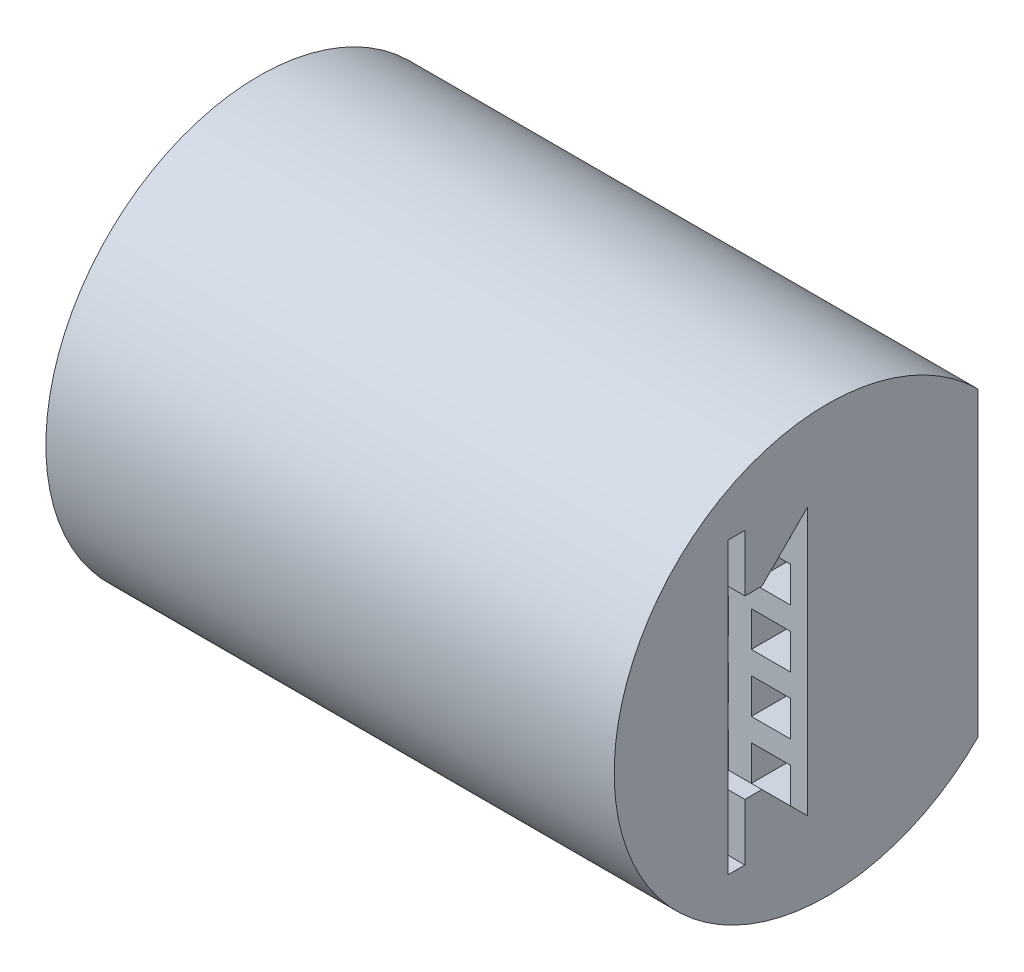
SolidWorks part; units mm, degrees
ref_plane "Front Plane" through (0, 0, 0) normal (0, 0, 1) x (1, 0, 0)
ref_plane "Top Plane" through (0, 0, 0) normal (0, 1, 0) x (1, 0, 0)
ref_plane "Right Plane" through (0, 0, 0) normal (1, 0, 0) x (0, 0, -1)
sketch "Sketch1" plane through (0, 0, 0) normal (1, 0, 0) x (0, 0, -1)
  line L1 (5.3033, 5.3033) -> (5.3033, -5.3033)
  line L14 (5.3033, 5.3033) -> (8.7403, 1.8663) construction
  line L15 (-3.5, -5.1) -> (-3.5, 5.1)
  line L16 (-3.5, 5.1) -> (-2.9, 5.1)
  line L17 (-2.9, 5.1) -> (-2.9, 3.1)
  line L18 (-2.9, 3.1) -> (-2.3, 3.1)
  line L19 (-2.3, 3.1) -> (-0.6967, 4.7033)
  line L20 (17.1404, 0) -> (-17.1404, 0) construction
  line L21 (-0.6967, 4.7033) -> (-0.6967, -4.7033)
  line L22 (-0.6967, 4.7033) -> (5.3033, 4.7033) construction
  line L23 (-3.5, -5.1) -> (-2.9, -5.1)
  line L24 (-2.9, -5.1) -> (-2.9, -3.1)
  line L25 (-2.9, -3.1) -> (-2.3, -3.1)
  line L26 (-2.3, -3.1) -> (-0.6967, -4.7033)
  circle A2 centre (0, 0) radius 7.5 construction
  arc A4 (5.3033, 5.3033) -> (5.3033, -5.3033) centre (0, 0) ccw
  point P13 (0, 0)
  point P14 (-17.1404, 0)
  point P15 (-1.4227, 0)
  point P17 (-3.1802, 0)
  point P18 (-0.7891, 0)
  point P20 (-3.5, 0)
  point P24 (-0.6967, 0)
  dimension "D2" = 45
  dimension "D1" = 15
  dimension "D3" = 5.1
  dimension "D4" = 0.6
  dimension "D5" = 2
  dimension "D6" = 0.6
  dimension "D7" = 45
  dimension "D8" = 0.6
  dimension "D9" = 6
extrude "Boss-Extrude1" add sketch "Sketch1" along normal mid plane 20
sketch "Sketch2" plane through (0, 0, -5.3033) normal (0, 0, -1) x (-1, 0, 0)
  line L0 (9.4, -4.7033) -> (9.4, 4.7033) construction
  line L1 (9.4, 4.7033) -> (-9.4, 4.7033) construction
  line L2 (-9.4, 4.7033) -> (-9.4, -4.7033) construction
  line L3 (-9.4, -4.7033) -> (9.4, -4.7033) construction
  line L4 (10, -5.3033) -> (10, 5.3033)
  line L5 (10, 5.3033) -> (-10, 5.3033)
  line L6 (-10, 5.3033) -> (-10, -5.3033)
  line L7 (-10, -5.3033) -> (10, -5.3033)
  line L8 (10, -5.3033) -> (10, 5.3033) construction
  line L9 (10, 5.3033) -> (-10, 5.3033) construction
  line L10 (-10, 5.3033) -> (-10, -5.3033) construction
  line L11 (-10, -5.3033) -> (10, -5.3033) construction
  line L12 (-7.2222, -4.7033) -> (-7.2222, -3.462)
  line L19 (-9.4, -4.7033) -> (-8.0222, -4.7033)
  line L20 (-9.4, -4.7033) -> (-9.4, -3.462)
  line L21 (-9.4, -3.462) -> (-8.0222, -3.462)
  line L22 (-8.0222, -4.7033) -> (-8.0222, -3.462)
  line L23 (-7.2222, -4.7033) -> (-5.8444, -4.7033)
  line L24 (-5.8444, -4.7033) -> (-5.8444, -3.462)
  line L25 (-7.2222, -3.462) -> (-5.8444, -3.462)
  line L26 (-7.2222, -2.662) -> (-7.2222, -1.4207)
  line L27 (-7.2222, -2.662) -> (-5.8444, -2.662)
  line L28 (-5.8444, -2.662) -> (-5.8444, -1.4207)
  line L29 (-7.2222, -1.4207) -> (-5.8444, -1.4207)
  line L30 (-7.2222, -0.6207) -> (-7.2222, 0.6207)
  line L31 (-7.2222, -0.6207) -> (-5.8444, -0.6207)
  line L32 (-5.8444, -0.6207) -> (-5.8444, 0.6207)
  line L33 (-7.2222, 0.6207) -> (-5.8444, 0.6207)
  line L34 (-9.4, -2.662) -> (-9.4, -1.4207)
  line L35 (-9.4, -2.662) -> (-8.0222, -2.662)
  line L36 (-8.0222, -2.662) -> (-8.0222, -1.4207)
  line L37 (-9.4, -1.4207) -> (-8.0222, -1.4207)
  line L38 (-9.4, -0.6207) -> (-9.4, 0.6207)
  line L39 (-9.4, -0.6207) -> (-8.0222, -0.6207)
  line L40 (-8.0222, -0.6207) -> (-8.0222, 0.6207)
  line L41 (-9.4, 0.6207) -> (-8.0222, 0.6207)
  line L42 (-5.0444, -4.7033) -> (-5.0444, -3.462)
  line L43 (-5.0444, -4.7033) -> (-3.6667, -4.7033)
  line L44 (-3.6667, -4.7033) -> (-3.6667, -3.462)
  line L45 (-5.0444, -3.462) -> (-3.6667, -3.462)
  line L46 (-2.8667, -4.7033) -> (-2.8667, -3.462)
  line L47 (-2.8667, -4.7033) -> (-1.4889, -4.7033)
  line L48 (-1.4889, -4.7033) -> (-1.4889, -3.462)
  line L49 (-2.8667, -3.462) -> (-1.4889, -3.462)
  line L50 (-0.6889, -4.7033) -> (-0.6889, -3.462)
  line L51 (-0.6889, -4.7033) -> (0.6889, -4.7033)
  line L52 (0.6889, -4.7033) -> (0.6889, -3.462)
  line L53 (-0.6889, -3.462) -> (0.6889, -3.462)
  line L54 (1.4889, -4.7033) -> (1.4889, -3.462)
  line L55 (1.4889, -4.7033) -> (2.8667, -4.7033)
  line L56 (2.8667, -4.7033) -> (2.8667, -3.462)
  line L57 (1.4889, -3.462) -> (2.8667, -3.462)
  line L58 (3.6667, -4.7033) -> (3.6667, -3.462)
  line L59 (3.6667, -4.7033) -> (5.0444, -4.7033)
  line L60 (5.0444, -4.7033) -> (5.0444, -3.462)
  line L61 (3.6667, -3.462) -> (5.0444, -3.462)
  line L62 (5.8444, -4.7033) -> (5.8444, -3.462)
  line L63 (5.8444, -4.7033) -> (7.2222, -4.7033)
  line L64 (7.2222, -4.7033) -> (7.2222, -3.462)
  line L65 (5.8444, -3.462) -> (7.2222, -3.462)
  line L66 (8.0222, -4.7033) -> (8.0222, -3.462)
  line L67 (8.0222, -4.7033) -> (9.4, -4.7033)
  line L68 (9.4, -4.7033) -> (9.4, -3.462)
  line L69 (8.0222, -3.462) -> (9.4, -3.462)
  line L82 (-5.0444, -2.662) -> (-5.0444, -1.4207)
  line L83 (-5.0444, -2.662) -> (-3.6667, -2.662)
  line L84 (-3.6667, -2.662) -> (-3.6667, -1.4207)
  line L85 (-5.0444, -1.4207) -> (-3.6667, -1.4207)
  line L86 (-2.8667, -2.662) -> (-2.8667, -1.4207)
  line L87 (-2.8667, -2.662) -> (-1.4889, -2.662)
  line L88 (-1.4889, -2.662) -> (-1.4889, -1.4207)
  line L89 (-2.8667, -1.4207) -> (-1.4889, -1.4207)
  line L90 (-0.6889, -2.662) -> (-0.6889, -1.4207)
  line L91 (-0.6889, -2.662) -> (0.6889, -2.662)
  line L92 (0.6889, -2.662) -> (0.6889, -1.4207)
  line L93 (-0.6889, -1.4207) -> (0.6889, -1.4207)
  line L94 (1.4889, -2.662) -> (1.4889, -1.4207)
  line L95 (1.4889, -2.662) -> (2.8667, -2.662)
  line L96 (2.8667, -2.662) -> (2.8667, -1.4207)
  line L97 (1.4889, -1.4207) -> (2.8667, -1.4207)
  line L98 (3.6667, -2.662) -> (3.6667, -1.4207)
  line L99 (3.6667, -2.662) -> (5.0444, -2.662)
  line L100 (5.0444, -2.662) -> (5.0444, -1.4207)
  line L101 (3.6667, -1.4207) -> (5.0444, -1.4207)
  line L102 (5.8444, -2.662) -> (5.8444, -1.4207)
  line L103 (5.8444, -2.662) -> (7.2222, -2.662)
  line L104 (7.2222, -2.662) -> (7.2222, -1.4207)
  line L105 (5.8444, -1.4207) -> (7.2222, -1.4207)
  line L106 (8.0222, -2.662) -> (8.0222, -1.4207)
  line L107 (8.0222, -2.662) -> (9.4, -2.662)
  line L108 (9.4, -2.662) -> (9.4, -1.4207)
  line L109 (8.0222, -1.4207) -> (9.4, -1.4207)
  line L122 (-5.0444, -0.6207) -> (-5.0444, 0.6207)
  line L123 (-5.0444, -0.6207) -> (-3.6667, -0.6207)
  line L124 (-3.6667, -0.6207) -> (-3.6667, 0.6207)
  line L125 (-5.0444, 0.6207) -> (-3.6667, 0.6207)
  line L126 (-2.8667, -0.6207) -> (-2.8667, 0.6207)
  line L127 (-2.8667, -0.6207) -> (-1.4889, -0.6207)
  line L128 (-1.4889, -0.6207) -> (-1.4889, 0.6207)
  line L129 (-2.8667, 0.6207) -> (-1.4889, 0.6207)
  line L130 (-0.6889, -0.6207) -> (-0.6889, 0.6207)
  line L131 (-0.6889, -0.6207) -> (0.6889, -0.6207)
  line L132 (0.6889, -0.6207) -> (0.6889, 0.6207)
  line L133 (-0.6889, 0.6207) -> (0.6889, 0.6207)
  line L134 (1.4889, -0.6207) -> (1.4889, 0.6207)
  line L135 (1.4889, -0.6207) -> (2.8667, -0.6207)
  line L136 (2.8667, -0.6207) -> (2.8667, 0.6207)
  line L137 (1.4889, 0.6207) -> (2.8667, 0.6207)
  line L138 (3.6667, -0.6207) -> (3.6667, 0.6207)
  line L139 (3.6667, -0.6207) -> (5.0444, -0.6207)
  line L140 (5.0444, -0.6207) -> (5.0444, 0.6207)
  line L141 (3.6667, 0.6207) -> (5.0444, 0.6207)
  line L142 (5.8444, -0.6207) -> (5.8444, 0.6207)
  line L143 (5.8444, -0.6207) -> (7.2222, -0.6207)
  line L144 (7.2222, -0.6207) -> (7.2222, 0.6207)
  line L145 (5.8444, 0.6207) -> (7.2222, 0.6207)
  line L146 (8.0222, -0.6207) -> (8.0222, 0.6207)
  line L147 (8.0222, -0.6207) -> (9.4, -0.6207)
  line L148 (9.4, -0.6207) -> (9.4, 0.6207)
  line L149 (8.0222, 0.6207) -> (9.4, 0.6207)
  line L150 (-9.4, 1.4207) -> (-9.4, 2.662)
  line L151 (-9.4, 1.4207) -> (-8.0222, 1.4207)
  line L152 (-8.0222, 1.4207) -> (-8.0222, 2.662)
  line L153 (-9.4, 2.662) -> (-8.0222, 2.662)
  line L154 (-7.2222, 1.4207) -> (-7.2222, 2.662)
  line L155 (-7.2222, 1.4207) -> (-5.8444, 1.4207)
  line L156 (-5.8444, 1.4207) -> (-5.8444, 2.662)
  line L157 (-7.2222, 2.662) -> (-5.8444, 2.662)
  line L158 (-5.0444, 1.4207) -> (-5.0444, 2.662)
  line L159 (-5.0444, 1.4207) -> (-3.6667, 1.4207)
  line L160 (-3.6667, 1.4207) -> (-3.6667, 2.662)
  line L161 (-5.0444, 2.662) -> (-3.6667, 2.662)
  line L162 (-2.8667, 1.4207) -> (-2.8667, 2.662)
  line L163 (-2.8667, 1.4207) -> (-1.4889, 1.4207)
  line L164 (-1.4889, 1.4207) -> (-1.4889, 2.662)
  line L165 (-2.8667, 2.662) -> (-1.4889, 2.662)
  line L166 (-0.6889, 1.4207) -> (-0.6889, 2.662)
  line L167 (-0.6889, 1.4207) -> (0.6889, 1.4207)
  line L168 (0.6889, 1.4207) -> (0.6889, 2.662)
  line L169 (-0.6889, 2.662) -> (0.6889, 2.662)
  line L170 (1.4889, 1.4207) -> (1.4889, 2.662)
  line L171 (1.4889, 1.4207) -> (2.8667, 1.4207)
  line L172 (2.8667, 1.4207) -> (2.8667, 2.662)
  line L173 (1.4889, 2.662) -> (2.8667, 2.662)
  line L174 (3.6667, 1.4207) -> (3.6667, 2.662)
  line L175 (3.6667, 1.4207) -> (5.0444, 1.4207)
  line L176 (5.0444, 1.4207) -> (5.0444, 2.662)
  line L177 (3.6667, 2.662) -> (5.0444, 2.662)
  line L178 (5.8444, 1.4207) -> (5.8444, 2.662)
  line L179 (5.8444, 1.4207) -> (7.2222, 1.4207)
  line L180 (7.2222, 1.4207) -> (7.2222, 2.662)
  line L181 (5.8444, 2.662) -> (7.2222, 2.662)
  line L182 (8.0222, 1.4207) -> (8.0222, 2.662)
  line L183 (8.0222, 1.4207) -> (9.4, 1.4207)
  line L184 (9.4, 1.4207) -> (9.4, 2.662)
  line L185 (8.0222, 2.662) -> (9.4, 2.662)
  line L186 (-9.4, 3.462) -> (-9.4, 4.7033)
  line L187 (-9.4, 3.462) -> (-8.0222, 3.462)
  line L188 (-8.0222, 3.462) -> (-8.0222, 4.7033)
  line L189 (-9.4, 4.7033) -> (-8.0222, 4.7033)
  line L190 (-7.2222, 3.462) -> (-7.2222, 4.7033)
  line L191 (-7.2222, 3.462) -> (-5.8444, 3.462)
  line L192 (-5.8444, 3.462) -> (-5.8444, 4.7033)
  line L193 (-7.2222, 4.7033) -> (-5.8444, 4.7033)
  line L194 (-5.0444, 3.462) -> (-5.0444, 4.7033)
  line L195 (-5.0444, 3.462) -> (-3.6667, 3.462)
  line L196 (-3.6667, 3.462) -> (-3.6667, 4.7033)
  line L197 (-5.0444, 4.7033) -> (-3.6667, 4.7033)
  line L198 (-2.8667, 3.462) -> (-2.8667, 4.7033)
  line L199 (-2.8667, 3.462) -> (-1.4889, 3.462)
  line L200 (-1.4889, 3.462) -> (-1.4889, 4.7033)
  line L201 (-2.8667, 4.7033) -> (-1.4889, 4.7033)
  line L202 (-0.6889, 3.462) -> (-0.6889, 4.7033)
  line L203 (-0.6889, 3.462) -> (0.6889, 3.462)
  line L204 (0.6889, 3.462) -> (0.6889, 4.7033)
  line L205 (-0.6889, 4.7033) -> (0.6889, 4.7033)
  line L206 (1.4889, 3.462) -> (1.4889, 4.7033)
  line L207 (1.4889, 3.462) -> (2.8667, 3.462)
  line L208 (2.8667, 3.462) -> (2.8667, 4.7033)
  line L209 (1.4889, 4.7033) -> (2.8667, 4.7033)
  line L210 (3.6667, 3.462) -> (3.6667, 4.7033)
  line L211 (3.6667, 3.462) -> (5.0444, 3.462)
  line L212 (5.0444, 3.462) -> (5.0444, 4.7033)
  line L213 (3.6667, 4.7033) -> (5.0444, 4.7033)
  line L214 (5.8444, 3.462) -> (5.8444, 4.7033)
  line L215 (5.8444, 3.462) -> (7.2222, 3.462)
  line L216 (7.2222, 3.462) -> (7.2222, 4.7033)
  line L217 (5.8444, 4.7033) -> (7.2222, 4.7033)
  line L218 (8.0222, 3.462) -> (8.0222, 4.7033)
  line L219 (8.0222, 3.462) -> (9.4, 3.462)
  line L220 (9.4, 3.462) -> (9.4, 4.7033)
  line L221 (8.0222, 4.7033) -> (9.4, 4.7033)
  point P184 (-9.4, 3.3033)
  point P187 (9.2773, 4.5714)
  dimension "D3" = 9
  dimension "D4" = 5
  dimension "D5" = 0.8
  dimension "D6" = 0.8
  dimension "D1" = 0
  dimension "D2" = 0.6
extrude "Cut-Extrude1" cut sketch "Sketch2" against normal up to next (6 mm away)
